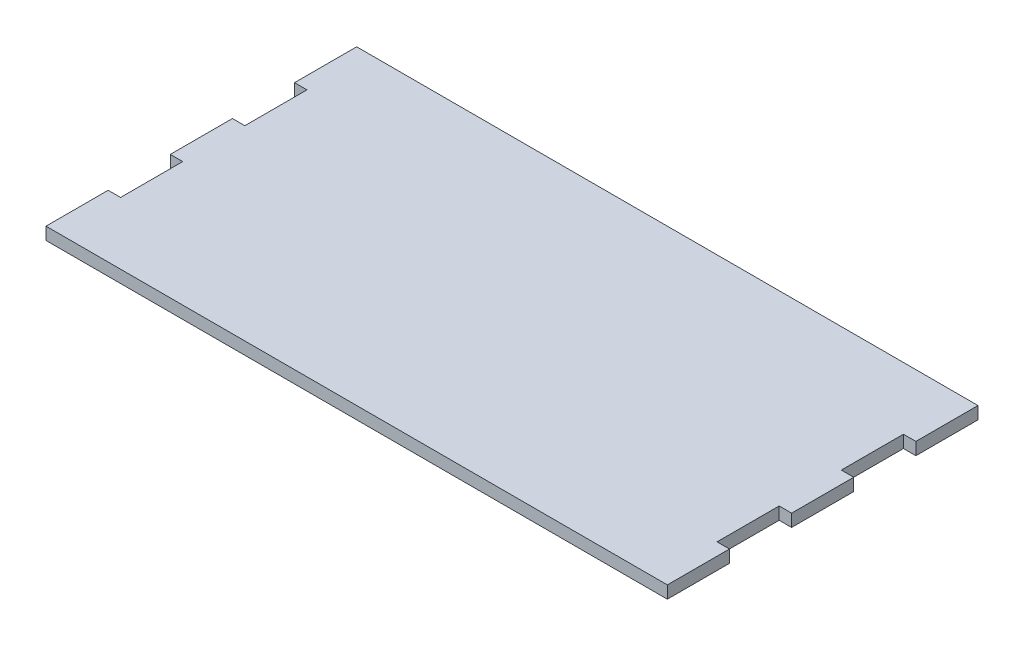
SolidWorks part; units mm, degrees
ref_plane "Front Plane" through (0, 0, 0) normal (0, 0, 1) x (1, 0, 0)
ref_plane "Top Plane" through (0, 0, 0) normal (0, 1, 0) x (1, 0, 0)
ref_plane "Right Plane" through (0, 0, 0) normal (1, 0, 0) x (0, 0, -1)
sketch "Sketch3" plane through (0, 0, 0) normal (0, 1, 0) x (1, 0, 0)
  line L1 (0, 0) -> (250, 0)
  line L2 (0, 0) -> (0, 125)
  line L3 (0, 125) -> (250, 125)
  line L4 (250, 0) -> (250, 125)
  dimension "D1" = 250
  dimension "D2" = 125
extrude "Boss-Extrude1" add sketch "Sketch3" along normal blind 5
sketch "Sketch10" plane through (0, 5, 0) normal (0, 1, 0) x (1, 0, 0)
  line L0 (0, 125) -> (0, 0) construction
  line L1 (250, 125) -> (0, 125) construction
  line L3 (125, 125) -> (125, 0) construction
  line L4 (0, 0) -> (250, 0) construction
  line L5 (0, 100) -> (5, 100)
  line L6 (0, 100) -> (0, 75)
  line L7 (0, 75) -> (5, 75)
  line L8 (5, 100) -> (5, 75)
  line L9 (250, 50) -> (245, 50)
  line L10 (0, 50) -> (5, 50)
  line L11 (0, 50) -> (0, 25)
  line L12 (0, 25) -> (5, 25)
  line L13 (5, 50) -> (5, 25)
  line L14 (245, 50) -> (245, 25)
  line L15 (250, 50) -> (250, 25)
  line L16 (250, 25) -> (245, 25)
  line L17 (250, 75) -> (245, 75)
  line L18 (250, 100) -> (245, 100)
  line L19 (250, 100) -> (250, 75)
  line L20 (245, 100) -> (245, 75)
  dimension "D1" = 25
  dimension "D2" = 25
  dimension "D3" = 25
  dimension "D4" = 25
  dimension "D5" = 5
  dimension "D6" = 5
extrude "Cut-Extrude4" cut sketch "Sketch10" against normal through all
sketch "Sketch11" plane through (0, 0, 0) normal (0, -1, 0) x (1, 0, 0)
  line L0 (0, 0) -> (250, 0) construction
  line L1 (5, -10) -> (245, -10)
  line L2 (5, -10) -> (5, -15)
  line L3 (5, -15) -> (245, -15)
  line L4 (245, -10) -> (245, -15)
  line L5 (5, -25) -> (5, 0) construction
  line L6 (245, -25) -> (245, 0) construction
  dimension "D1" = 5
  dimension "D2" = 10
extrude "Cut-Extrude5" cut sketch "Sketch11" against normal blind 2.5
